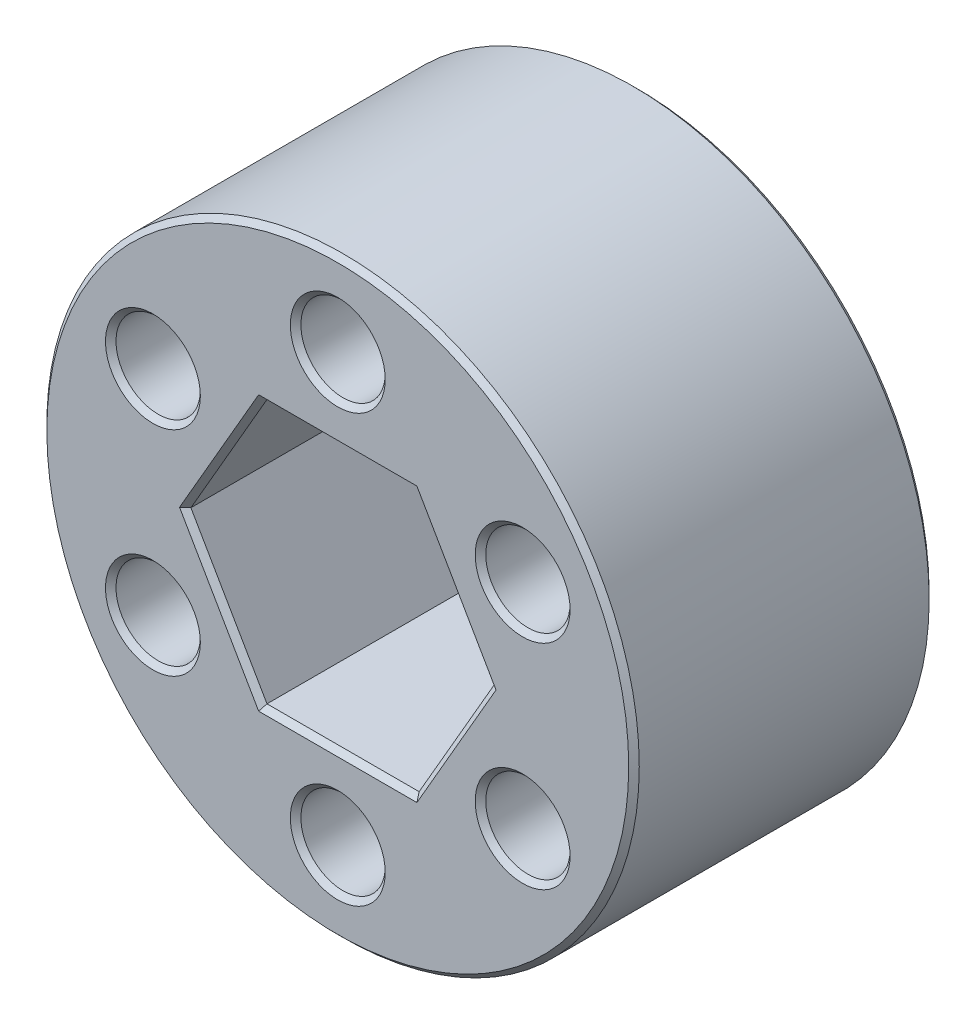
SolidWorks part; units mm, degrees
ref_plane "Front Plane" through (0, 0, 0) normal (0, 0, 1) x (1, 0, 0)
ref_plane "Top Plane" through (0, 0, 0) normal (0, 1, 0) x (1, 0, 0)
ref_plane "Right Plane" through (0, 0, 0) normal (1, 0, 0) x (0, 0, -1)
sketch "Sketch1" plane through (0, 0, 0) normal (0, 0, 1) x (1, 0, 0)
  line L1 (-7.3323, 0) -> (-3.6662, -6.35)
  line L2 (-3.6662, -6.35) -> (3.6662, -6.35)
  line L3 (3.6662, -6.35) -> (7.3323, 0)
  line L4 (7.3323, 0) -> (3.6662, 6.35)
  line L5 (3.6662, 6.35) -> (-3.6662, 6.35)
  line L6 (-3.6662, 6.35) -> (-7.3323, 0)
  circle A0 centre (0, 0) radius 14.2748
  circle A1 centre (0, 0) radius 6.35 construction
  circle A2 centre (0, 10.287) radius 2.032
  circle A3 centre (8.9088, 5.1435) radius 2.032
  circle A4 centre (8.9088, -5.1435) radius 2.032
  circle A5 centre (0, -10.287) radius 2.032
  circle A6 centre (-8.9088, -5.1435) radius 2.032
  circle A7 centre (-8.9088, 5.1435) radius 2.032
  point P13 (-9.6715, 5.4338)
  point P14 (0, 0)
  point P24 (0, 0)
  point P25 (0, 0)
  dimension "D1" = 28.5496
  dimension "D2" = 12.7
  dimension "D3" = 4.064
  dimension "D5" = 20.574
  dimension "D4" = 6
extrude "Boss-Extrude1" add sketch "Sketch1" along normal blind 14.478
chamfer "Chamfer1" distance 0.254 angle 45 26 edges at (-6.8768, 5.1435, 0) (-6.8768, -5.1435, 0) (2.032, -10.287, 0) (10.9408, -5.1435, 0) (10.9408, 5.1435, 0) (2.032, 10.287, 0) (0, 6.35, 0) (5.4993, 3.175, 0) (5.4993, -3.175, 0) (0, -6.35, 0) (-5.4993, -3.175, 0) (-5.4993, 3.175, 0) (14.2748, 0, 0) (-6.8768, 5.1435, 14.478) (2.032, -10.287, 14.478) (10.9408, 5.1435, 14.478) (0, -6.35, 14.478) (5.4993, -3.175, 14.478) (5.4993, 3.175, 14.478) (0, 6.35, 14.478) (-5.4993, 3.175, 14.478) (-5.4993, -3.175, 14.478) (14.2748, 0, 14.478) (2.032, 10.287, 14.478) (10.9408, -5.1435, 14.478) (-6.8768, -5.1435, 14.478)
